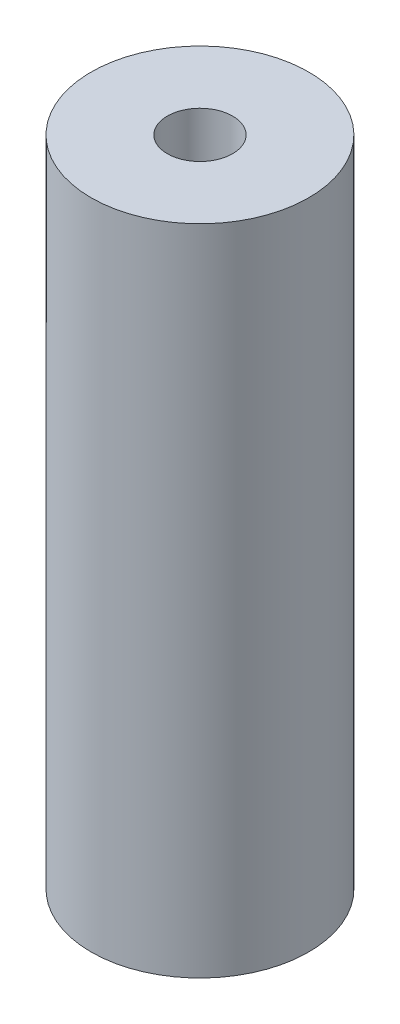
SolidWorks part; units mm, degrees
ref_plane "Alzado" through (0, 0, 0) normal (0, 0, 1) x (1, 0, 0)
ref_plane "Planta" through (0, 0, 0) normal (0, 1, 0) x (1, 0, 0)
ref_plane "Vista lateral" through (0, 0, 0) normal (1, 0, 0) x (0, 0, -1)
sketch "Croquis1" plane through (0, 0, 0) normal (0, 1, 0) x (1, 0, 0)
  circle A0 centre (0, 0) radius 5
  dimension "D1" = 10
extrude "Saliente-Extruir1" add sketch "Croquis1" along normal blind 30
sketch "Croquis2" plane through (0, 30, 0) normal (0, 1, 0) x (1, 0, 0)
  circle A0 centre (0, 0) radius 1.5
  dimension "D1" = 3
extrude "Cortar-Extruir1" cut sketch "Croquis2" against normal blind 5
sketch "Croquis4" plane through (0, 0, 0) normal (0, -1, 0) x (1, 0, 0)
  circle A0 centre (0, 0) radius 1.5
  dimension "D1" = 3
extrude "Cortar-Extruir2" cut sketch "Croquis4" against normal blind 5
